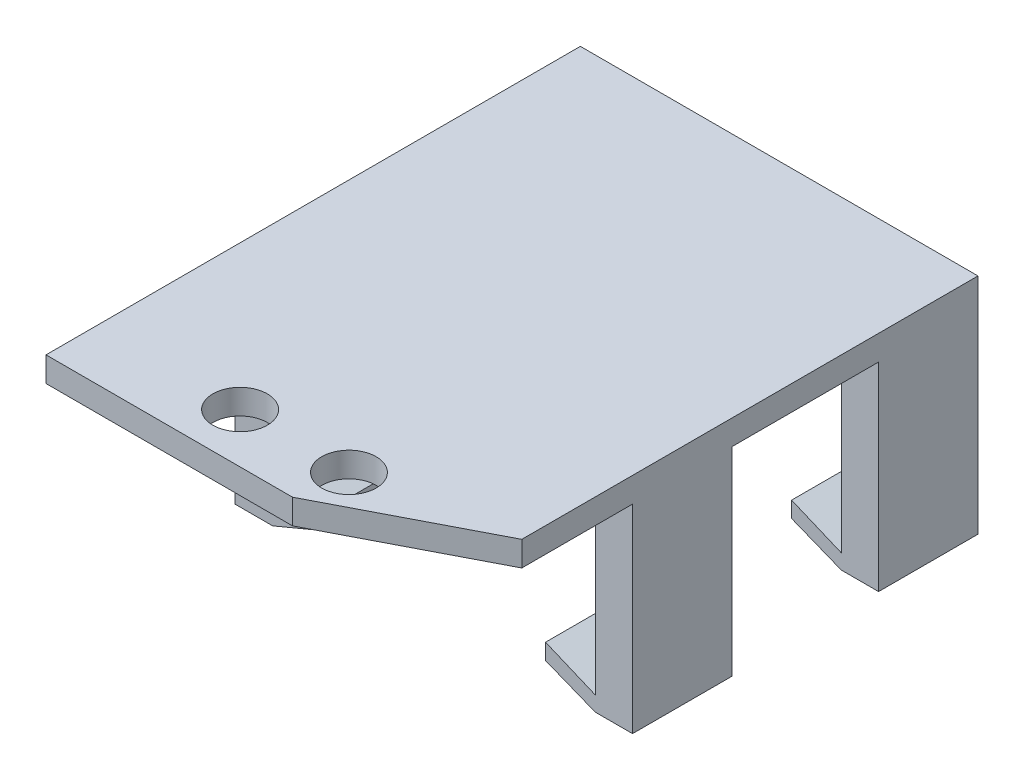
SolidWorks part; units mm, degrees
material "Custom Plastic"
ref_plane "Front Plane" through (0, 0, 0) normal (0, 0, 1) x (1, 0, 0)
ref_plane "Top Plane" through (0, 0, 0) normal (0, 1, 0) x (1, 0, 0)
ref_plane "Right Plane" through (0, 0, 0) normal (1, 0, 0) x (0, 0, -1)
sketch "Sketch3" plane through (0, 0, 0) normal (0, 1, 0) x (1, 0, 0)
  line L0 (29.1227, -39.629) -> (18.8853, -29.3915) construction
  line L1 (-11.5173, 12.441) -> (29.1227, 12.441)
  line L2 (-11.5173, 12.441) -> (-11.5173, -42.169)
  line L3 (-11.5173, -42.169) -> (18.8853, -42.169)
  line L4 (29.1227, 12.441) -> (29.1227, -34.5642)
  line L6 (21.4177, -26.8591) -> (29.1227, -34.5642) construction
  line L12 (18.8853, -42.169) -> (29.1227, -42.169)
  line L13 (29.1227, -42.169) -> (29.1227, -34.5642)
  circle A0 centre (3.2401, -37.089) radius 2.7813
  circle A2 centre (14.3653, -37.089) radius 2.7813
  dimension "D2" = 5.5626
  dimension "D3" = 5.5626
  dimension "D1" = 5.08
  dimension "1" = 40.64
  dimension "D4" = 11.1252
  dimension "D7" = 5.08
  dimension "D9" = 135
  dimension "D10" = 14.478
  dimension "D11" = 3.5814
extrude "Boss-Extrude3" add sketch "Sketch3" along normal blind 2.54
sketch "Sketch4" plane through (0, 0, 0) normal (0, -1, 0) x (1, 0, 0)
  line L0 (-11.5173, -12.441) -> (-11.5173, 42.169) construction
  line L1 (-11.5173, 27.945) -> (-7.7073, 27.945)
  line L2 (-11.5173, 27.945) -> (-11.5173, -12.441)
  line L3 (-11.5173, -12.441) -> (-7.7073, -12.441)
  line L4 (-7.7073, 27.945) -> (-7.7073, -12.441)
  line L5 (29.1227, -12.441) -> (-11.5173, -12.441) construction
  line L6 (-11.5173, 42.169) -> (29.1227, 42.169) construction
  line L7 (29.1227, 42.169) -> (29.1227, -12.441) construction
  line L8 (29.1227, 27.945) -> (25.3127, 27.945)
  line L9 (29.1227, 27.945) -> (29.1227, -12.441)
  line L10 (29.1227, -12.441) -> (25.3127, -12.441)
  line L11 (25.3127, 27.945) -> (25.3127, -12.441)
  dimension "D1" = 14.224
  dimension "D2" = 3.81
  dimension "D3" = 14.224
  dimension "D4" = 3.81
extrude "Boss-Extrude4" add sketch "Sketch4" along normal blind 20.32
sketch "Sketch5" plane through (-7.7073, 0, 0) normal (1, 0, 0) x (0, 0, -1)
  line L0 (-27.945, -20.32) -> (-27.945, 0) construction
  line L1 (-27.945, -18.796) -> (12.441, -18.796)
  line L2 (-27.945, -18.796) -> (-27.945, -20.32)
  line L3 (-27.945, -20.32) -> (12.441, -20.32)
  line L4 (12.441, -18.796) -> (12.441, -20.32)
  dimension "D1" = 1.524
extrude "Boss-Extrude5" add sketch "Sketch5" along normal blind 5.08
sketch "Sketch6" plane through (25.3127, 0, 0) normal (-1, 0, 0) x (0, 0, 1)
  line L0 (-12.441, 2.54) -> (-12.441, -20.32) construction
  line L1 (-12.441, -18.796) -> (27.945, -18.796)
  line L2 (-12.441, -18.796) -> (-12.441, -20.32)
  line L3 (-12.441, -20.32) -> (27.945, -20.32)
  line L4 (27.945, -18.796) -> (27.945, -20.32)
  dimension "D1" = 1.524
extrude "Boss-Extrude6" add sketch "Sketch6" along normal blind 5.08
sketch "Sketch7" plane through (0, 0, 27.945) normal (0, 0, 1) x (1, 0, 0)
  line L1 (-11.5173, 0) -> (29.1227, 0)
  line L2 (-11.5173, 0) -> (-11.5173, -20.32)
  line L3 (-11.5173, -20.32) -> (29.1227, -20.32)
  line L4 (29.1227, 0) -> (29.1227, -20.32)
extrude "Cut-Extrude1" cut sketch "Sketch7" against normal blind 5.08
sketch "Sketch11" plane through (0, 0, 0) normal (0, -1, 0) x (1, 0, 0)
  line L1 (-11.5173, 22.865) -> (29.1227, 22.865)
  line L2 (-11.5173, 22.865) -> (-11.5173, -12.441)
  line L3 (-11.5173, -12.441) -> (29.1227, -12.441)
  line L4 (29.1227, 22.865) -> (29.1227, -12.441)
extrude "Boss-Extrude7" add sketch "Sketch11" along normal blind 2.9718
sketch "Sketch12" plane through (0, 0, 22.865) normal (0, 0, 1) x (1, 0, 0)
  line L0 (-7.7073, -18.796) -> (-2.5934, -16.6688)
  line L1 (-2.5934, -16.6688) -> (-2.6273, -18.796)
  line L2 (-2.6273, -18.796) -> (-7.7073, -18.796)
  line L3 (20.2327, -18.796) -> (20.2327, -16.6688)
  line L4 (20.2327, -16.6688) -> (25.3127, -18.796)
  line L5 (25.3127, -18.796) -> (20.2327, -18.796)
  dimension "D1" = 2.1272
  dimension "D2" = 2.1272
extrude "Boss-Extrude8" add sketch "Sketch12" against normal up to surface (35.306 mm away) up to face at (8.8027, -13.1106, -12.441)
sketch "Sketch8" plane through (29.1227, 0, 0) normal (1, 0, 0) x (0, 0, -1)
  line L0 (12.441, -20.32) -> (-22.865, -20.32) construction
  line L1 (2.281, -20.32) -> (-12.705, -20.32)
  line L2 (2.281, -20.32) -> (2.281, 0)
  line L3 (2.281, 0) -> (-12.705, 0)
  line L4 (-12.705, -20.32) -> (-12.705, 0)
  line L5 (-42.169, 0) -> (-22.865, 0) construction
  line L6 (-22.865, -20.32) -> (-22.865, 0) construction
  line L7 (12.441, 2.54) -> (12.441, -20.32) construction
  dimension "D1" = 0
  dimension "D2" = 10.16
  dimension "D3" = 10.16
extrude "Cut-Extrude2" cut sketch "Sketch8" against normal through all
sketch "Sketch13" plane through (0, 0, 22.865) normal (0, 0, 1) x (1, 0, 0)
  line L0 (-7.6607, -20.32) -> (-2.618, -18.2165)
  line L1 (-11.5173, -20.32) -> (-2.6273, -20.32) construction
  line L2 (-2.6273, -18.796) -> (-2.5934, -16.6688) construction
  line L3 (-2.618, -18.2165) -> (-2.6273, -20.32)
  line L4 (-2.6273, -20.32) -> (-7.6607, -20.32)
  line L5 (20.2327, -20.32) -> (20.2048, -20.32)
  line L6 (20.2327, -20.32) -> (29.1227, -20.32) construction
  line L7 (20.2048, -20.32) -> (20.2327, -18.2946)
  line L8 (20.2327, -20.32) -> (20.2327, -16.6688) construction
  line L9 (20.2327, -18.2946) -> (20.2327, -20.32)
  line L10 (20.2327, -18.2946) -> (25.3127, -20.32)
  line L11 (25.3127, -20.32) -> (20.2327, -20.32)
  line M5 (20.2327, -16.6688) -> (20.2327, -20.32)
  line M6 (20.2327, -20.32) -> (29.1227, -20.32)
  line M10 (-11.5173, -20.32) -> (-2.6273, -20.32)
  line M11 (-2.6273, -20.32) -> (-2.6273, -18.796)
  line M12 (-2.6273, -18.796) -> (-2.5934, -16.6688)
  dimension "D1" = 2.1035
  dimension "D2" = 2.0254
extrude "Cut-Extrude3" cut sketch "Sketch13" against normal through all contours L0 M10 M11 M12 | L10 M5 M6
sketch "Sketch14" plane through (0, 0, 0) normal (0, -1, 0) x (1, 0, 0)
  circle A0 centre (3.2401, 37.089) radius 2.7813
  circle A1 centre (14.3653, 37.089) radius 2.7813
  circle A2 centre (3.2401, 37.089) radius 3.81
  circle A3 centre (14.3653, 37.089) radius 3.81
  dimension "D1" = 5.5626
  dimension "D2" = 5.5626
  dimension "D3" = 7.62
  dimension "D4" = 7.62
extrude "Boss-Extrude9" add sketch "Sketch14" against normal blind 2.54
sketch "Sketch15" plane through (0, 2.54, 0) normal (0, 1, 0) x (1, 0, 0)
  line L0 (18.8853, -42.169) -> (13.6783, -42.169) construction
  line L1 (-11.5173, -42.169) -> (29.1227, -42.169) construction
  line L2 (13.6783, -42.169) -> (29.1227, -42.169)
  line L4 (13.6783, -42.169) -> (18.8853, -39.4766)
  line L7 (13.6783, -42.169) -> (29.1227, -34.1831)
  line L8 (29.1227, -42.169) -> (29.1227, 12.441) construction
  line L9 (29.1227, -42.169) -> (29.1227, -34.1831)
  line L10 (8.8027, 12.441) -> (8.8027, -50.2652) construction
  line L11 (29.1227, 12.441) -> (-11.5173, 12.441) construction
  line L12 (3.9272, -42.169) -> (-11.5173, -34.1831)
  line L13 (-11.5173, -42.169) -> (-11.5173, -34.1831)
  line L14 (3.9272, -42.169) -> (-11.5173, -42.169)
  line M6 (-11.5173, -42.169) -> (29.1227, -42.169)
  line M10 (29.1227, -42.169) -> (29.1227, 12.441)
extrude "Cut-Extrude4" cut sketch "Sketch15" against normal through all contours L7 L4 M6 M10
equation "\"D3@Sketch8\"=\"D2@Sketch8\""
